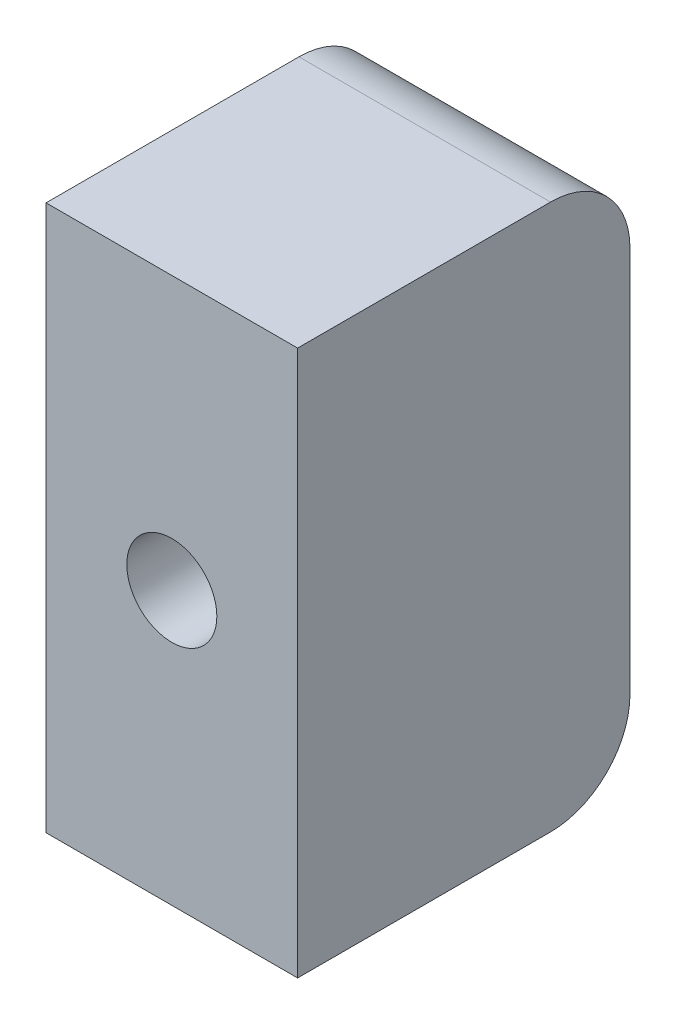
SolidWorks part; units mm, degrees
material "AISI 1020"
ref_plane "Спереди" through (0, 0, 0) normal (0, 0, 1) x (1, 0, 0)
ref_plane "Сверху" through (0, 0, 0) normal (0, 1, 0) x (1, 0, 0)
ref_plane "Справа" through (0, 0, 0) normal (1, 0, 0) x (0, 0, -1)
sketch "Эскиз1" plane through (0, 0, 0) normal (1, 0, 0) x (0, 0, -1)
  line L0 (-6, 9.4) -> (-25.1, 9.4) construction
  line L1 (0, 44.6) -> (0, 15.4) construction
  line L2 (-25.1, 50.6) -> (-6, 50.6) construction
  line L3 (-6, 9.4) -> (-25.1, 9.4)
  line L4 (0, 44.6) -> (0, 15.4)
  line L5 (-25.1, 50.6) -> (-6, 50.6)
  line L6 (-25.1, 50.6) -> (-25.1, 9.4)
  arc A0 (-6, 9.4) -> (0, 15.4) centre (-6, 15.4) ccw construction
  arc A1 (0, 44.6) -> (-6, 50.6) centre (-6, 44.6) ccw construction
  arc A2 (-6, 9.4) -> (0, 15.4) centre (-6, 15.4) ccw
  arc A3 (0, 44.6) -> (-6, 50.6) centre (-6, 44.6) ccw
extrude "Бобышка-Вытянуть1" add sketch "Эскиз1" against normal up to surface (19 mm away)
sketch3d "Трехмерный эскиз1"
  line L0 (-19, 15.4, 0) -> (0, 44.6, 0)
hole_wizard "Отверстие обработанное метчиком M8x1.251" positions "Эскиз2" profile "Эскиз3" tap size "M8x1.25" standard "Ansi Metric"
sketch "Эскиз2" plane through (0, 0, 0) normal (0, 0, -1) x (-1, 0, 0)
  line L0 (19, 15.4) -> (0, 44.6) construction
  point P0 (9.5, 30)
sketch "Эскиз3" plane through (-9.5, 30, 0) normal (1, 0, 0) x (0, 1, 0)
  line L0 (0, 0) -> (0, 30.2929)
  line L1 (0, 30.2929) -> (3.4, 28.25)
  line L2 (3.4, 28.25) -> (3.4, 0.85)
  line L3 (3.4, 0.85) -> (4.25, 0)
  line L5 (4.25, 0) -> (0, 0)
  line L6 (-3.4, 0.85) -> (-4.25, 0) construction
  line L10 (0, 30.2929) -> (-3.4, 28.25) construction
  line L11 (0, -6.35) -> (0, 107.95) construction
  dimension "Диаметр сверла" = 6.8
  dimension "Глубина сверла" = 28.25
  dimension "Диаметр передней зенковки" = 8.5
  dimension "Угол передней зенковки" = 90
  dimension "Угол заточки сверла" = 118
cosmetic thread "Отверстие резьбы1" parameters "D1"=22, "D2"=8
